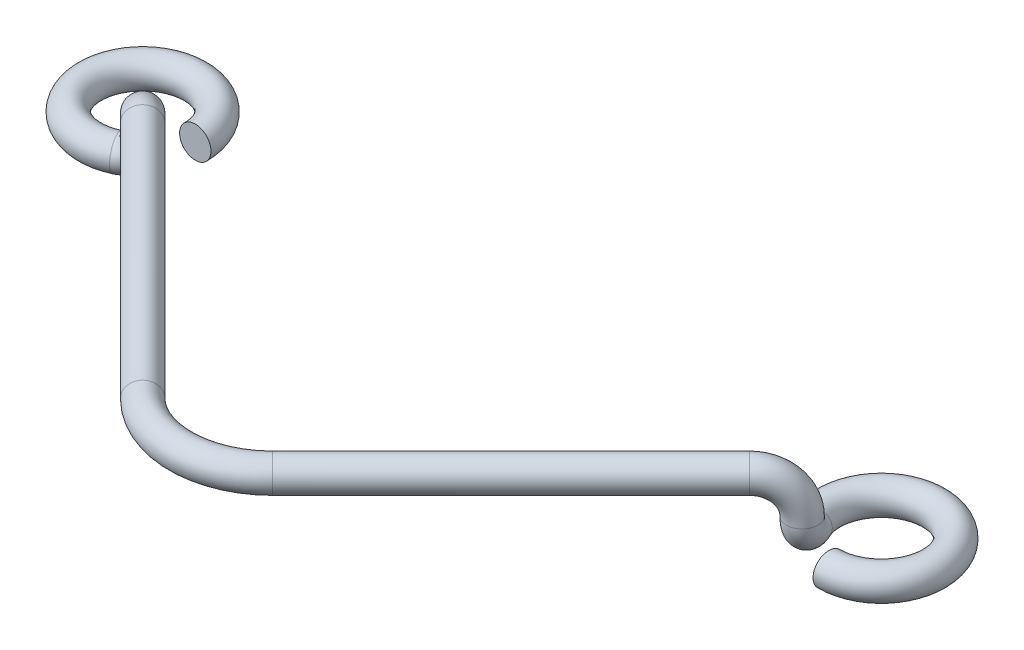
SolidWorks part; units mm, degrees
ref_plane "Front" through (0, 0, 0) normal (0, 0, 1) x (1, 0, 0)
ref_plane "Top" through (0, 0, 0) normal (0, 1, 0) x (1, 0, 0)
ref_plane "Right" through (0, 0, 0) normal (1, 0, 0) x (0, 0, -1)
sketch "Support-Top" plane through (0, 0, 0) normal (0, 1, 0) x (1, 0, 0)
  line L0 (0, 0) -> (0, 20) construction
  line L1 (0, 20) -> (-20, 20) construction
  line L2 (0, 0) -> (-20, 20) construction
  line L3 (-20, 20) -> (-18.7955, 17.417) construction
  line L4 (0, 0) -> (0, -20) construction
  line L5 (0, 20) -> (20, 20) construction
  line L6 (20, 20) -> (0, 0) construction
  line L7 (20, 20) -> (17.417, 18.7955) construction
  line L8 (20, 20) -> (20, 17.15) construction
  circle A0 centre (-20, 20) radius 2.85
  circle A1 centre (20, 20) radius 2.85
  point P2 (20, 17.15)
  point P8 (-17.15, 20)
  point P11 (17.417, 18.7955)
  point P12 (-18.7955, 17.417)
  dimension "Diam-Fixing-Hole" = 5.7
  dimension "D1" = 20
  dimension "CC-Fix" = 40
  dimension "D5" = 20
  dimension "Total-Width" = 40
sketch "Support-Front-Diam" plane through (0, 0, 0) normal (0, 0, 1) x (1, 0, 0)
  circle A0 centre (-17.15, 0) radius 0.85
  dimension "Diam" = 1.7
ref_plane "Plane1" through (0, 0, 0) normal (-0.7071, 0, 0.7071) x (0.0069, 1, 0.0069)
ref_plane "Plane8" through (0, 0, 0) normal (-0.7071, 0, -0.7071) x (-0.5774, -0.5774, 0.5774)
ref_plane "Plane4" through (-18.7955, 0, -17.417) normal (0.9063, 0, -0.4226) x (-0.4226, 0, -0.9063)
ref_plane "Plane6" through (17.417, 0, -18.7955) normal (0.4226, 0, 0.9063) x (0.9063, 0, -0.4226)
sketch "Support-Axle-1" plane through (-18.7955, 0, -17.417) normal (0.9063, 0, -0.4226) x (-0.4226, 0, -0.9063)
  line L0 (0, 0) -> (0, 2.2853) construction
sketch "Support-Axle-2" plane through (17.417, 0, -18.7955) normal (0.4226, 0, 0.9063) x (0.9063, 0, -0.4226)
  line L0 (0, 0) -> (0, 3.8924) construction
ref_plane "Plane5" through (-10.0281, 0, -21.5053) normal (-0.4226, 0, -0.9063) x (-0.9063, 0, 0.4226)
ref_plane "Plane7" through (21.5053, 0, -10.0281) normal (0.9063, 0, -0.4226) x (-0.4226, 0, -0.9063)
sketch "Support-Font-1" plane through (-10.0281, 0, -21.5053) normal (-0.4226, 0, -0.9063) x (-0.9063, 0, 0.4226)
  line L0 (12.5238, 0) -> (6.8238, 0) construction
  line L1 (8.6365, 1.0373) -> (8.6365, 0) construction
  arc A0 (9.6738, 0) -> (8.6365, 1.0373) centre (9.6738, 1.0373) cw
sketch "Support-Front-2" plane through (21.5053, 0, -10.0281) normal (0.9063, 0, -0.4226) x (-0.4226, 0, -0.9063)
  line L0 (8.6365, 1.0373) -> (8.6365, 0) construction
  line L3 (12.5238, 0) -> (6.8238, 0) construction
  arc A0 (9.6738, 0) -> (8.6365, 1.0373) centre (9.6738, 1.0373) cw
sketch "Support-Right-1" plane through (0, 0, 0) normal (-0.7071, 0, 0.7071) x (0.0069, 1, 0.0069)
  line L0 (-0.2773, 28.2829) -> (2.8227, 28.2829) construction
  line L1 (2.8227, 28.2829) -> (2.8227, 23.2668) construction
  line L2 (0.7897, 25.2603) -> (-0.2476, 25.2502) construction
  line L3 (2.8227, 23.2668) -> (3.0018, 5)
  line L4 (2.9122, 14.1334) -> (2.0622, 14.1334) construction
  line L6 (0, 0) -> (-0.2773, 28.2829) construction
  circle A1 centre (0.8094, 23.2471) radius 2.0134
  dimension "Height" = 3.1
  dimension "Dist-Center" = 5
  dimension "Diam-Half" = 0.85
ref_plane "Plane2" through (0, 3.0507, 0) normal (0, 1, 0) x (-1, 0, 0)
ref_plane "Ref-Plane" through (0, 2.2007, 0) normal (0, 1, 0) x (-1, 0, 0)
sketch "Support-Top-End" plane through (0, 3.0507, 0) normal (0, 1, 0) x (-1, 0, 0)
  line L0 (0, 0) -> (0, -20) construction
  line L1 (16.4318, -16.4318) -> (3.5146, -3.5146) construction
  line L2 (0, 0) -> (0, -6.4181) construction
  arc A0 (3.5146, -3.5146) -> (-3.5146, -3.5146) centre (0, -7.0291) ccw
sketch "Support-Right-2" plane through (0, 0, 0) normal (-0.7071, 0, -0.7071) x (-0.5774, -0.5774, 0.5774)
  line L0 (-20.7351, -10.9256) -> (-5.8196, -0.3788)
  line L1 (-20.7351, -10.9256) -> (-24.8553, -13.8391) construction
  line L2 (-24.8553, -13.8391) -> (-23.094, -16.3299) construction
  line L4 (-23.094, -16.3299) -> (0, 0) construction
  circle A0 centre (-19.5726, -12.5695) radius 2.0134
  ellipse E0 centre (-21.5062, -13.9368) end of major axis (-20.9073, -14.7837) minor radius 0.3548 (-20.9073, -14.7837) -> (-21.2165, -13.7319) ccw construction
ref_plane "Plane3" through (0, 0, -20) normal (0, 0, 1) x (1, 0, 0)
sketch "Sketch12" plane through (-10.0281, 0, -21.5053) normal (-0.4226, 0, -0.9063) x (-0.9063, 0, 0.4226)
  arc A0 (8.6365, 1.0373) -> (9.6738, 0) centre (9.6738, 1.0373) ccw construction
  arc A1 (8.6365, 1.0373) -> (9.6738, 0) centre (9.6738, 1.0373) ccw
sketch "Sketch4" plane through (0, 0, -20) normal (0, 0, 1) x (1, 0, 0)
  circle A0 centre (-17.15, 0) radius 0.85 construction
  circle A1 centre (-17.15, 0) radius 0.85
sketch "Sketch17" plane through (0, 0, 0) normal (0, 1, 0) x (1, 0, 0)
  line L0 (20, 20) -> (17.417, 18.7955) construction
  line L1 (20, 20) -> (20, 17.15) construction
  line L2 (20, 20) -> (17.417, 18.7955) construction
  line L3 (20, 20) -> (20, 17.15) construction
  circle A0 centre (20, 20) radius 2.85 construction
  arc A1 (20, 17.15) -> (17.417, 18.7955) centre (20, 20) ccw
sketch "Sketch18" plane through (21.5053, 0, -10.0281) normal (0.9063, 0, -0.4226) x (-0.4226, 0, -0.9063)
  arc A0 (8.6365, 1.0373) -> (9.6738, 0) centre (9.6738, 1.0373) ccw construction
  arc A1 (8.6365, 1.0373) -> (9.6738, 0) centre (9.6738, 1.0373) ccw
sketch "Sketch19" plane through (0, 0, 0) normal (-0.7071, 0, -0.7071) x (-0.5774, -0.5774, 0.5774)
  line L0 (-20.7351, -10.9256) -> (-5.8196, -0.3788) construction
  line L1 (-20.7351, -10.9256) -> (-5.8196, -0.3788)
  line L2 (-21.2165, -13.7319) -> (-20.6177, -14.5789) construction
  line L3 (-21.2165, -13.7319) -> (-20.6177, -14.5789) construction
  circle A0 centre (-19.5726, -12.5695) radius 2.0134 construction
  arc A1 (-20.7351, -10.9256) -> (-21.2165, -13.7319) centre (-19.5726, -12.5695) ccw
sketch "Sketch5" plane through (0, 0, 0) normal (0, 1, 0) x (1, 0, 0)
  line L0 (0, 20) -> (-20, 20) construction
  line L1 (0, 0) -> (-20, 20) construction
  line L2 (0, 20) -> (-20, 20) construction
  line L3 (0, 0) -> (-20, 20) construction
  circle A0 centre (-20, 20) radius 2.85 construction
  arc A1 (-17.15, 20) -> (-18.7955, 17.417) centre (-20, 20) ccw
sketch "Sketch7" plane through (0, 0, 0) normal (-0.7071, 0, 0.7071) x (0.0069, 1, 0.0069)
  line L1 (2.8227, 23.2668) -> (3.0018, 5) construction
  line L2 (2.8227, 23.2668) -> (3.0018, 5)
  circle A0 centre (0.8094, 23.2471) radius 2.0134 construction
  arc A2 (2.8227, 23.2668) -> (0.7897, 25.2603) centre (0.8094, 23.2471) ccw
sketch "Sketch9" plane through (0, 3.0507, 0) normal (0, 1, 0) x (-1, 0, 0)
  arc A0 (3.5146, -3.5146) -> (-3.5146, -3.5146) centre (0, -7.0291) ccw construction
  arc A1 (3.5146, -3.5146) -> (-3.5146, -3.5146) centre (0, -7.0291) ccw
curve "CompCurve1"
sweep "Body" add profiles "Sketch4" path "CompCurve1"
equation "\"Diam-Half@Support-Right-1\" = \"Diam@Support-Front-Diam\" / 2"
